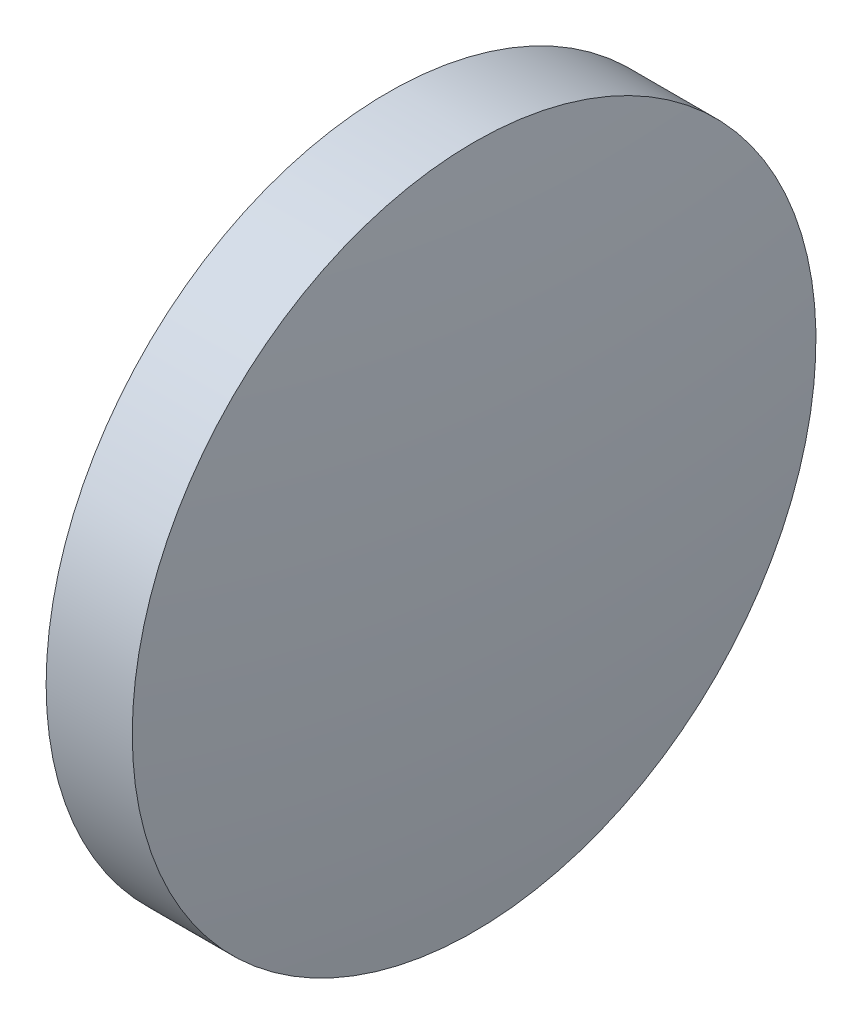
SolidWorks part; units mm, degrees
ref_plane "前视基准面" through (0, 0, 0) normal (0, 0, 1) x (1, 0, 0)
ref_plane "上视基准面" through (0, 0, 0) normal (0, 1, 0) x (1, 0, 0)
ref_plane "右视基准面" through (0, 0, 0) normal (1, 0, 0) x (0, 0, -1)
sketch "草图1" plane through (0, 0, 0) normal (0, 0, 1) x (1, 0, 0)
  line L0 (208.2754, 4.5067) -> (217.6734, 4.5067) construction
  line L1 (211.1445, 4.5067) -> (211.1445, 10.8567)
  line L2 (213.1445, 4.5067) -> (211.1445, 4.5067)
  line L5 (211.1445, 10.8567) -> (212.7445, 10.8567)
  arc A0 (213.1445, 4.5067) -> (212.7445, 10.8567) centre (162.5414, 4.5067) ccw
revolve "旋转1" add sketch "草图1" angle 360 about L0
